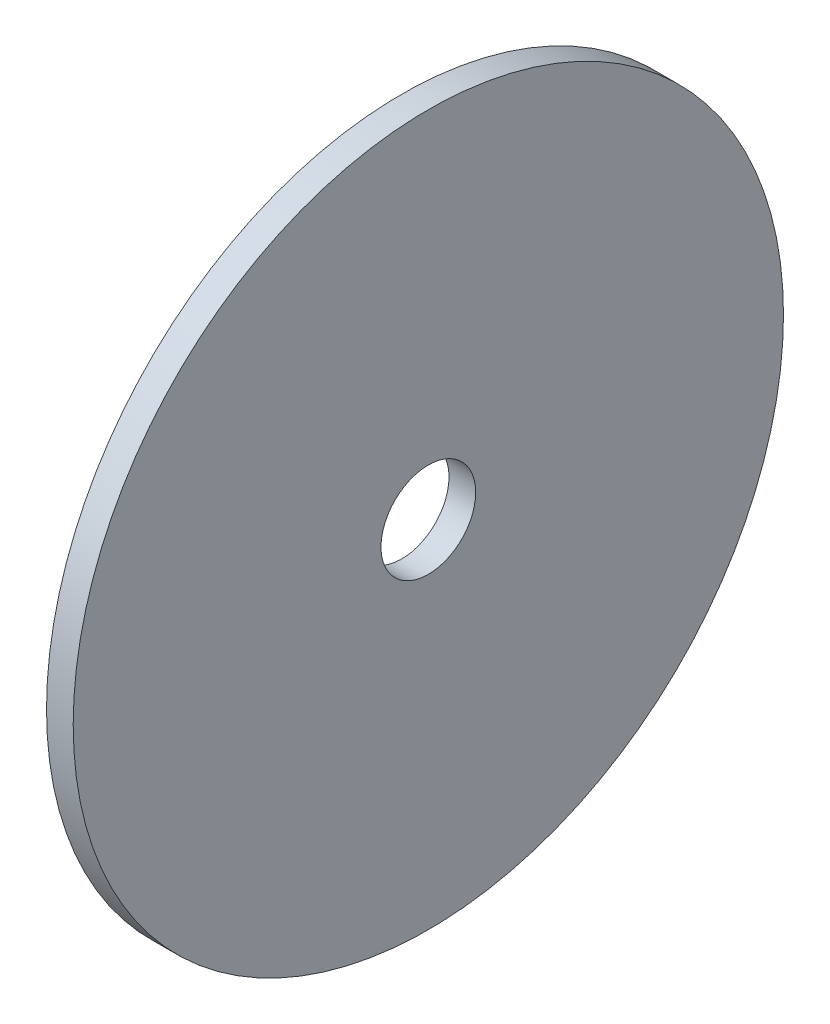
SolidWorks part; units mm, degrees
material "Acier S235"
ref_plane "Plan de face" through (0, 0, 0) normal (0, 0, 1) x (1, 0, 0)
ref_plane "Plan de dessus" through (0, 0, 0) normal (0, 1, 0) x (1, 0, 0)
ref_plane "Plan de droite" through (0, 0, 0) normal (1, 0, 0) x (0, 0, -1)
sketch "Esquisse8" plane through (0, 0, 0) normal (1, 0, 0) x (0, 0, -1)
  circle A0 centre (0, 0) radius 7.1
  circle A1 centre (0, 0) radius 53.25
  dimension "D1" = 14.2
  dimension "D2" = 106.5
extrude "Boss.-Extru.2" add sketch "Esquisse8" along normal blind 4 from offset 96 separate body
